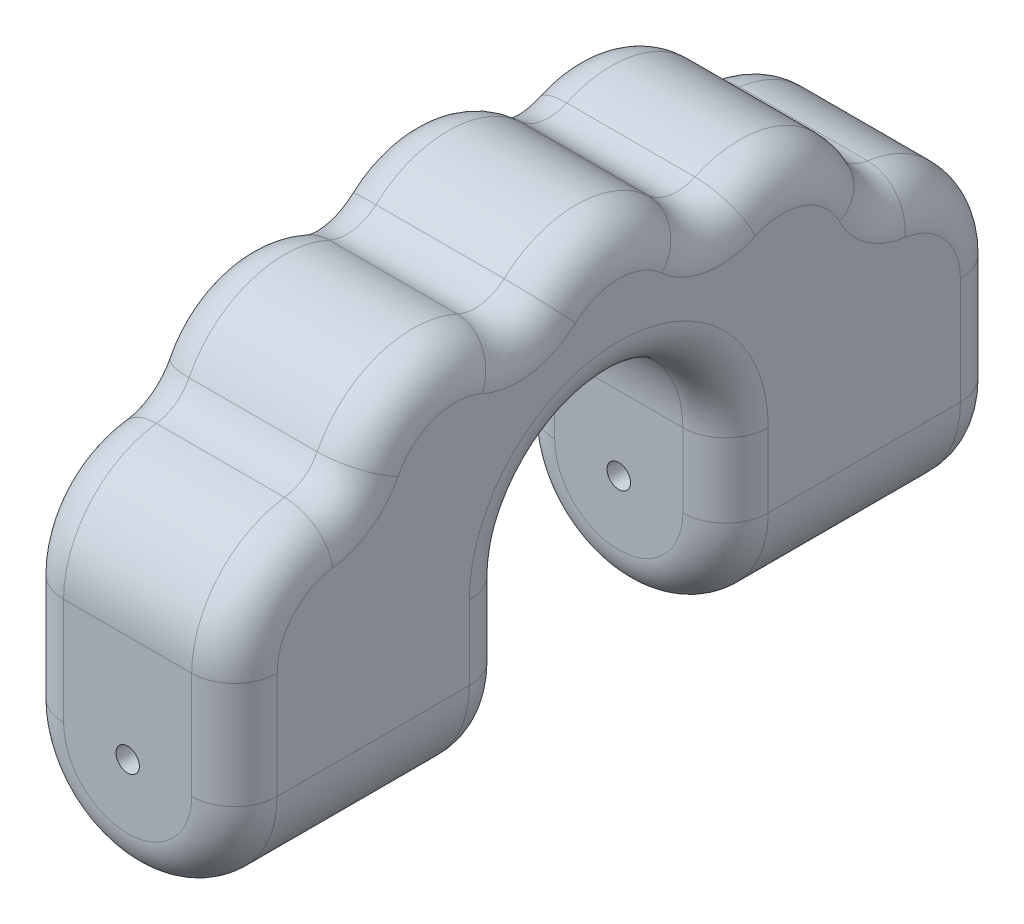
SolidWorks part; units mm, degrees
ref_plane "Спереди" through (0, 0, 0) normal (0, 0, 1) x (1, 0, 0)
ref_plane "Сверху" through (0, 0, 0) normal (0, 1, 0) x (1, 0, 0)
ref_plane "Справа" through (0, 0, 0) normal (1, 0, 0) x (0, 0, -1)
sketch "Эскиз1" plane through (0, 0, 0) normal (0, 0, 1) x (1, 0, 0)
  line L0 (-2.5, 0) -> (-2.5, 7.5)
  line L1 (-2.5, 7.5) -> (2.5, 7.5)
  line L2 (2.5, 7.5) -> (2.5, 0)
  arc A0 (-2.5, 0) -> (2.5, 0) centre (0, 0) ccw
  dimension "D1" = 5
  dimension "D2" = 7.5
extrude "Бобышка-Вытянуть1" add sketch "Эскиз1" along normal blind 18
sketch "Эскиз2" plane through (2.5, 0, 0) normal (1, 0, 0) x (0, 0, -1)
  line L0 (-9, 7.5) -> (-9, -2.0073) construction
  line L1 (-18, 7.5) -> (0, 7.5) construction
  line L2 (0, 0) -> (0, 7.5) construction
  line L3 (-18, 0) -> (0, 0) construction
  line L4 (-18, 2.5) -> (-18, 8.1505)
  line L5 (-18, 8.1505) -> (0, 8.1505)
  line L6 (0, 8.1505) -> (0, 2.5)
  line L7 (-11.5, 1.7305) -> (-11.5, -3.556)
  line L8 (-11.5, -3.556) -> (-6.5, -3.556)
  line L9 (-6.5, -3.556) -> (-6.5, 1.7305)
  arc A0 (-6.8431, 6.264) -> (-11.1569, 6.264) centre (-9, 5) ccw
  arc A1 (-2.7426, 4.9882) -> (-6.8431, 6.264) centre (-5.1732, 4.4035) ccw
  arc A2 (0, 2.5) -> (-2.7426, 4.9882) centre (-2.5, 2.5) ccw
  arc A3 (-18, 2.5) -> (-15.2574, 4.9882) centre (-15.5, 2.5) cw
  arc A4 (-15.2574, 4.9882) -> (-11.1569, 6.264) centre (-12.8268, 4.4035) cw
  arc A5 (-6.5, 1.7305) -> (-11.5, 1.7305) centre (-9, 1.7305) ccw
  dimension "D1" = 5
  dimension "D2" = 5
  dimension "D3" = 5
  dimension "D4" = 5
extrude "Вырез-Вытянуть1" cut sketch "Эскиз2" against normal through all
sketch "Эскиз3" plane through (0, 0, 0) normal (0, 0, -1) x (-1, 0, 0)
  circle A0 centre (0, 0) radius 0.2744
extrude "Вырез-Вытянуть2" cut sketch "Эскиз3" against normal through all
fillet "Скругление1" radius 1 4 edges at (0, 4.9882, 2.7426) (0, 6.264, 6.8431) (0, 6.264, 11.1569) (0, 4.9882, 15.2574)
fillet "Скругление2" radius 1 32 edges at (0, -2.5, 0) (-2.5, 1.25, 0) (-2.5, 4.1484, 0.6205) (-2.5, 5.1555, 2.6234) (-2.5, 6.7625, 4.3453) (-2.5, 6.5944, 6.7916) (-2.5, 7.5, 9) (-2.5, 6.5944, 11.2084) (-2.5, 6.7625, 13.6547) (-2.5, 5.1555, 15.3766) (-2.5, 4.1484, 17.3795) (-2.5, 1.25, 18) (0, -2.5, 18) (0, -2.5, 6.5) (-2.5, 0.8652, 6.5) (-2.5, 4.2305, 9) (-2.5, 0.8652, 11.5) (0, -2.5, 11.5) (2.5, 0.8652, 11.5) (2.5, 1.25, 18) (2.5, 4.1484, 17.3795) (2.5, 5.1555, 15.3766) (2.5, 6.7625, 13.6547) (2.5, 6.5944, 11.2084) (2.5, 7.5, 9) (2.5, 6.5944, 6.7916) (2.5, 6.7625, 4.3453) (2.5, 5.1555, 2.6234) (2.5, 4.1484, 0.6205) (2.5, 1.25, 0) (2.5, 0.8652, 6.5) (2.5, 4.2305, 9)
